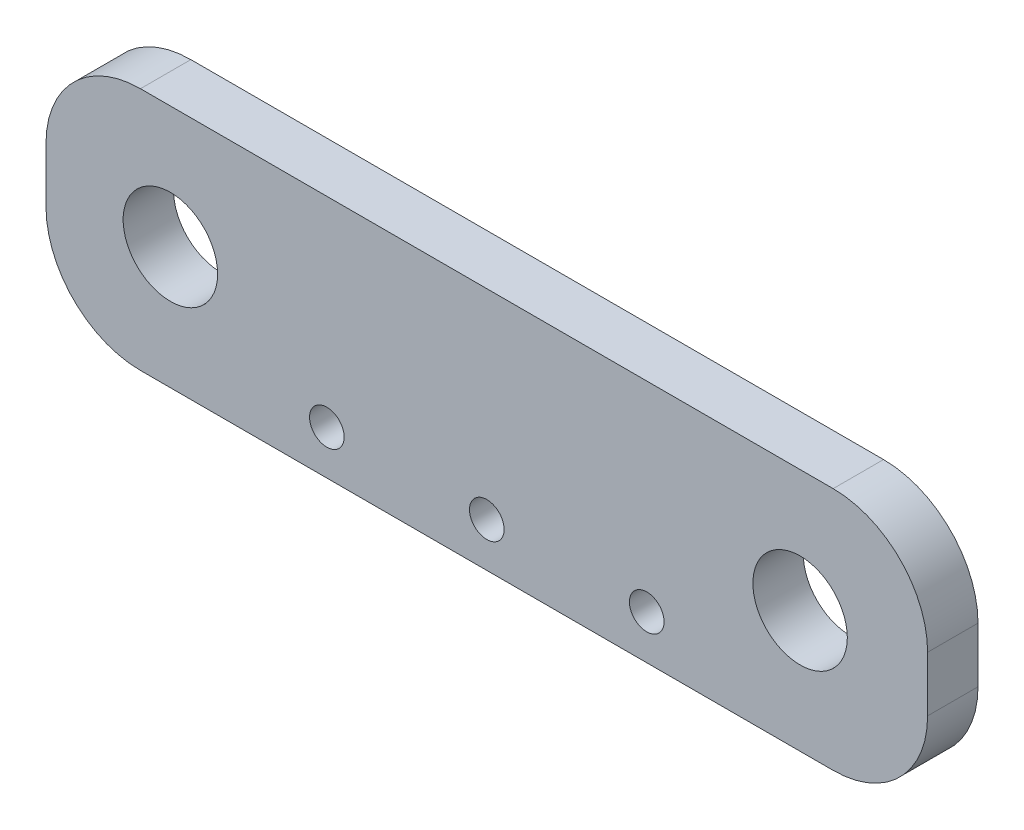
SolidWorks part; units mm, degrees
ref_plane "Front Plane" through (0, 0, 0) normal (0, 0, 1) x (1, 0, 0)
ref_plane "Top Plane" through (0, 0, 0) normal (0, 1, 0) x (1, 0, 0)
ref_plane "Right Plane" through (0, 0, 0) normal (1, 0, 0) x (0, 0, -1)
sketch "Sketch1" plane through (0, 0, 0) normal (0, 0, 1) x (1, 0, 0)
  line L1 (-14, -3.875) -> (14, -3.875)
  line L2 (-14, -3.875) -> (-14, 3.875)
  line L3 (-14, 3.875) -> (14, 3.875)
  line L4 (14, -3.875) -> (14, 3.875)
  line L5 (-14, -3.875) -> (14, 3.875) construction
  line L6 (-14, 3.875) -> (14, -3.875) construction
  point P0 (0, 0)
  dimension "D1" = 28
  dimension "D2" = 7.75
extrude "Boss-Extrude1" add sketch "Sketch1" along normal blind 1.6
sketch "Sketch2" plane through (0, 0, 1.6) normal (0, 0, 1) x (1, 0, 0)
  line L0 (-1000, 0) -> (49000, 0) construction
  line L1 (-14, 3.875) -> (-14, -3.875) construction
  circle A0 centre (-10.05, 0) radius 1.5
  circle A1 centre (9.95, 0) radius 1.5
  dimension "D3" = 3
  dimension "D4" = 3
  dimension "D1" = 3.95
  dimension "D2" = 23.95
extrude "Cut-Extrude1" cut sketch "Sketch2" against normal through all
sketch "Sketch3" plane through (0, 0, 1.6) normal (0, 0, 1) x (1, 0, 0)
  line L0 (0, -1000) -> (0, 49000) construction
  line L1 (-1000, -2.475) -> (49000, -2.475) construction
  line L2 (-14, -3.875) -> (14, -3.875) construction
  circle A0 centre (0, -2.475) radius 0.55
  circle A1 centre (-5.08, -2.475) radius 0.55
  circle A2 centre (5.08, -2.475) radius 0.55
  dimension "D2" = 1.1
  dimension "D3" = 1.1
  dimension "D4" = 1.1
  dimension "D1" = 1.4
  dimension "D5" = 5.08
  dimension "D6" = 5.08
extrude "Cut-Extrude2" cut sketch "Sketch3" against normal through all
fillet "Fillet1" radius 3 4 edges at (14, 3.875, 0.8) (14, -3.875, 0.8) (-14, 3.875, 0.8) (-14, -3.875, 0.8)
